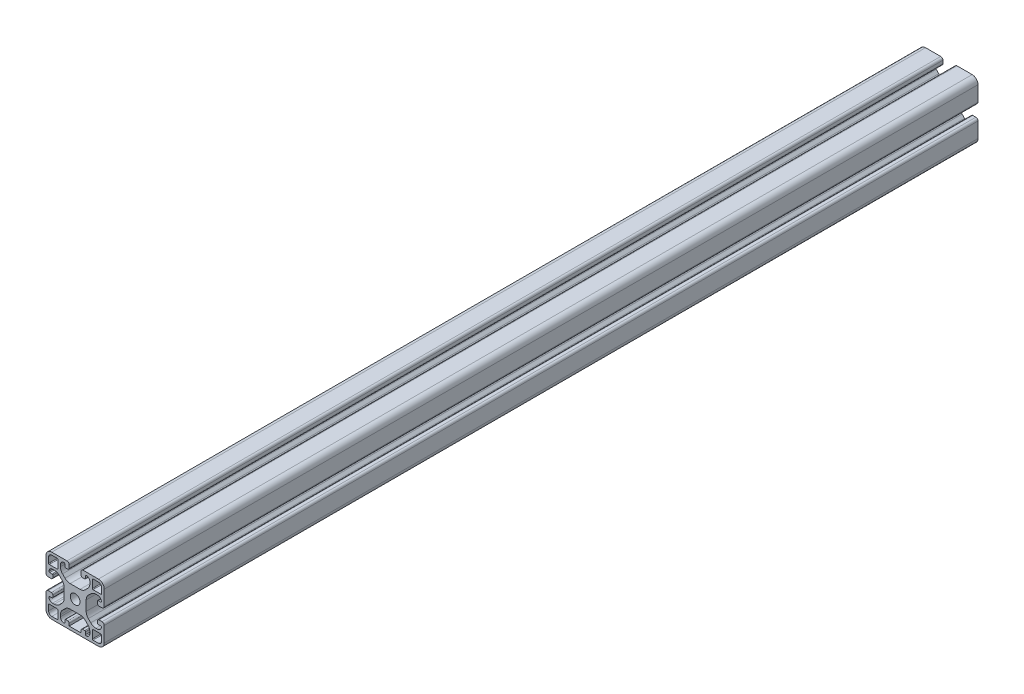
SolidWorks part; units mm, degrees
ref_plane "Ebene vorne" through (0, 0, 0) normal (0, 0, 1) x (1, 0, 0)
ref_plane "Ebene oben" through (0, 0, 0) normal (0, 1, 0) x (1, 0, 0)
ref_plane "Ebene rechts" through (0, 0, 0) normal (1, 0, 0) x (0, 0, -1)
ref_plane "Ebene1" through (0, 0, 1000) normal (0, 0, 1) x (1, 0, 0)
sketch "Skizze1" plane through (0, 0, 1000) normal (0, 0, 1) x (1, 0, 0)
  line L0 (27.8, 32.3) -> (27.8, 37.7)
  line L1 (28.3, 38.2) -> (32, 38.2)
  line L2 (34.2, 36) -> (34.2, 32.3)
  line L3 (33.7, 31.8) -> (28.3, 31.8)
  line L4 (28.3, 8.2) -> (33.7, 8.2)
  line L5 (34.2, 7.7) -> (34.2, 4)
  line L6 (32, 1.8) -> (28.3, 1.8)
  line L7 (27.8, 2.3) -> (27.8, 7.7)
  line L8 (3.7, 31.8) -> (-1.7, 31.8)
  line L9 (-2.2, 32.3) -> (-2.2, 36)
  line L10 (0, 38.2) -> (3.7, 38.2)
  line L11 (4.2, 37.7) -> (4.2, 32.3)
  line L12 (4.2, 7.7) -> (4.2, 2.3)
  line L13 (3.7, 1.8) -> (0, 1.8)
  line L14 (-2.2, 4) -> (-2.2, 7.7)
  line L15 (-1.7, 8.2) -> (3.7, 8.2)
  line L16 (20.1, 2) -> (11.9, 2)
  line L17 (11.9, 2) -> (11.9, 3.65)
  line L18 (10.9, 4.65) -> (9.4, 4.65)
  line L19 (8.9, 4.15) -> (8.9, 2.5)
  line L20 (5.9, 4.5) -> (5.9, 5.7076)
  line L21 (7.3645, 9.2431) -> (9.0569, 10.9355)
  line L22 (12.5924, 12.4) -> (19.4076, 12.4)
  line L23 (22.9431, 10.9355) -> (24.6355, 9.2431)
  line L24 (26.1, 5.7076) -> (26.1, 4.5)
  line L25 (23.1, 2.5) -> (23.1, 4.15)
  line L26 (22.6, 4.65) -> (21.1, 4.65)
  line L27 (20.1, 3.65) -> (20.1, 2)
  line L28 (5.9, 34.2924) -> (5.9, 35.5)
  line L29 (8.9, 37.5) -> (8.9, 35.85)
  line L30 (9.4, 35.35) -> (10.9, 35.35)
  line L31 (11.9, 36.35) -> (11.9, 38.5)
  line L32 (10.4, 40) -> (0, 40)
  line L33 (-4, 36) -> (-4, 25.6)
  line L34 (-2.5, 24.1) -> (-0.35, 24.1)
  line L35 (0.65, 25.1) -> (0.65, 26.6)
  line L36 (0.15, 27.1) -> (-1.5, 27.1)
  line L37 (0.5, 30.1) -> (1.7076, 30.1)
  line L38 (5.2431, 28.6355) -> (6.9355, 26.9431)
  line L39 (8.4, 23.4076) -> (8.4, 16.5924)
  line L40 (6.9355, 13.0569) -> (5.2431, 11.3645)
  line L41 (1.7076, 9.9) -> (0.5, 9.9)
  line L42 (-1.5, 12.9) -> (0.15, 12.9)
  line L43 (0.65, 13.4) -> (0.65, 14.9)
  line L44 (-0.35, 15.9) -> (-2.5, 15.9)
  line L45 (-4, 14.4) -> (-4, 4)
  line L46 (0, 0) -> (32, 0)
  line L47 (36, 4) -> (36, 14.4)
  line L48 (34.5, 15.9) -> (32.35, 15.9)
  line L49 (31.35, 14.9) -> (31.35, 13.4)
  line L50 (31.85, 12.9) -> (33.5, 12.9)
  line L51 (31.5, 9.9) -> (30.2924, 9.9)
  line L52 (26.7569, 11.3645) -> (25.0645, 13.0569)
  line L53 (23.6, 16.5924) -> (23.6, 23.4076)
  line L54 (25.0645, 26.9431) -> (26.7569, 28.6355)
  line L55 (30.2924, 30.1) -> (31.5, 30.1)
  line L56 (33.5, 27.1) -> (31.85, 27.1)
  line L57 (31.35, 26.6) -> (31.35, 25.1)
  line L58 (32.35, 24.1) -> (34.5, 24.1)
  line L59 (36, 25.6) -> (36, 36)
  line L60 (32, 40) -> (21.6, 40)
  line L61 (20.1, 38.5) -> (20.1, 36.35)
  line L62 (21.1, 35.35) -> (22.6, 35.35)
  line L63 (23.1, 35.85) -> (23.1, 37.5)
  line L64 (26.1, 35.5) -> (26.1, 34.2924)
  line L65 (24.6355, 30.7569) -> (22.9431, 29.0645)
  line L66 (19.4076, 27.6) -> (12.5924, 27.6)
  line L67 (9.0569, 29.0645) -> (7.3645, 30.7569)
  circle A0 centre (16, 20) radius 3.35
  arc A1 (28.3, 31.8) -> (27.8, 32.3) centre (28.3, 32.3) cw
  arc A2 (27.8, 37.7) -> (28.3, 38.2) centre (28.3, 37.7) cw
  arc A3 (32, 38.2) -> (34.2, 36) centre (32, 36) cw
  arc A4 (34.2, 32.3) -> (33.7, 31.8) centre (33.7, 32.3) cw
  arc A5 (27.8, 7.7) -> (28.3, 8.2) centre (28.3, 7.7) cw
  arc A6 (33.7, 8.2) -> (34.2, 7.7) centre (33.7, 7.7) cw
  arc A7 (34.2, 4) -> (32, 1.8) centre (32, 4) cw
  arc A8 (28.3, 1.8) -> (27.8, 2.3) centre (28.3, 2.3) cw
  arc A9 (4.2, 32.3) -> (3.7, 31.8) centre (3.7, 32.3) cw
  arc A10 (-1.7, 31.8) -> (-2.2, 32.3) centre (-1.7, 32.3) cw
  arc A11 (-2.2, 36) -> (0, 38.2) centre (0, 36) cw
  arc A12 (3.7, 38.2) -> (4.2, 37.7) centre (3.7, 37.7) cw
  arc A13 (3.7, 8.2) -> (4.2, 7.7) centre (3.7, 7.7) cw
  arc A14 (4.2, 2.3) -> (3.7, 1.8) centre (3.7, 2.3) cw
  arc A15 (0, 1.8) -> (-2.2, 4) centre (0, 4) cw
  arc A16 (-2.2, 7.7) -> (-1.7, 8.2) centre (-1.7, 7.7) cw
  arc A17 (11.9, 3.65) -> (10.9, 4.65) centre (10.9, 3.65) ccw
  arc A18 (9.4, 4.65) -> (8.9, 4.15) centre (9.4, 4.15) ccw
  arc A19 (8.9, 2.5) -> (8.4, 2) centre (8.4, 2.5) cw
  arc A20 (8.4, 2) -> (5.9, 4.5) centre (8.4, 4.5) cw
  arc A21 (5.9, 5.7076) -> (7.3645, 9.2431) centre (10.9, 5.7076) cw
  arc A22 (9.0569, 10.9355) -> (12.5924, 12.4) centre (12.5924, 7.4) cw
  arc A23 (19.4076, 12.4) -> (22.9431, 10.9355) centre (19.4076, 7.4) cw
  arc A24 (24.6355, 9.2431) -> (26.1, 5.7076) centre (21.1, 5.7076) cw
  arc A25 (26.1, 4.5) -> (23.6, 2) centre (23.6, 4.5) cw
  arc A26 (23.6, 2) -> (23.1, 2.5) centre (23.6, 2.5) cw
  arc A27 (23.1, 4.15) -> (22.6, 4.65) centre (22.6, 4.15) ccw
  arc A28 (21.1, 4.65) -> (20.1, 3.65) centre (21.1, 3.65) ccw
  arc A29 (7.3645, 30.7569) -> (5.9, 34.2924) centre (10.9, 34.2924) cw
  arc A30 (5.9, 35.5) -> (8.4, 38) centre (8.4, 35.5) cw
  arc A31 (8.4, 38) -> (8.9, 37.5) centre (8.4, 37.5) cw
  arc A32 (8.9, 35.85) -> (9.4, 35.35) centre (9.4, 35.85) ccw
  arc A33 (10.9, 35.35) -> (11.9, 36.35) centre (10.9, 36.35) ccw
  arc A34 (11.9, 38.5) -> (10.4, 40) centre (10.4, 38.5) ccw
  arc A35 (0, 40) -> (-4, 36) centre (0, 36) ccw
  arc A36 (-4, 25.6) -> (-2.5, 24.1) centre (-2.5, 25.6) ccw
  arc A37 (-0.35, 24.1) -> (0.65, 25.1) centre (-0.35, 25.1) ccw
  arc A38 (0.65, 26.6) -> (0.15, 27.1) centre (0.15, 26.6) ccw
  arc A39 (-1.5, 27.1) -> (-2, 27.6) centre (-1.5, 27.6) cw
  arc A40 (-2, 27.6) -> (0.5, 30.1) centre (0.5, 27.6) cw
  arc A41 (1.7076, 30.1) -> (5.2431, 28.6355) centre (1.7076, 25.1) cw
  arc A42 (6.9355, 26.9431) -> (8.4, 23.4076) centre (3.4, 23.4076) cw
  arc A43 (8.4, 16.5924) -> (6.9355, 13.0569) centre (3.4, 16.5924) cw
  arc A44 (5.2431, 11.3645) -> (1.7076, 9.9) centre (1.7076, 14.9) cw
  arc A45 (0.5, 9.9) -> (-2, 12.4) centre (0.5, 12.4) cw
  arc A46 (-2, 12.4) -> (-1.5, 12.9) centre (-1.5, 12.4) cw
  arc A47 (0.15, 12.9) -> (0.65, 13.4) centre (0.15, 13.4) ccw
  arc A48 (0.65, 14.9) -> (-0.35, 15.9) centre (-0.35, 14.9) ccw
  arc A49 (-2.5, 15.9) -> (-4, 14.4) centre (-2.5, 14.4) ccw
  arc A50 (-4, 4) -> (0, 0) centre (0, 4) ccw
  arc A51 (32, 0) -> (36, 4) centre (32, 4) ccw
  arc A52 (36, 14.4) -> (34.5, 15.9) centre (34.5, 14.4) ccw
  arc A53 (32.35, 15.9) -> (31.35, 14.9) centre (32.35, 14.9) ccw
  arc A54 (31.35, 13.4) -> (31.85, 12.9) centre (31.85, 13.4) ccw
  arc A55 (33.5, 12.9) -> (34, 12.4) centre (33.5, 12.4) cw
  arc A56 (34, 12.4) -> (31.5, 9.9) centre (31.5, 12.4) cw
  arc A57 (30.2924, 9.9) -> (26.7569, 11.3645) centre (30.2924, 14.9) cw
  arc A58 (25.0645, 13.0569) -> (23.6, 16.5924) centre (28.6, 16.5924) cw
  arc A59 (23.6, 23.4076) -> (25.0645, 26.9431) centre (28.6, 23.4076) cw
  arc A60 (26.7569, 28.6355) -> (30.2924, 30.1) centre (30.2924, 25.1) cw
  arc A61 (31.5, 30.1) -> (34, 27.6) centre (31.5, 27.6) cw
  arc A62 (34, 27.6) -> (33.5, 27.1) centre (33.5, 27.6) cw
  arc A63 (31.85, 27.1) -> (31.35, 26.6) centre (31.85, 26.6) ccw
  arc A64 (31.35, 25.1) -> (32.35, 24.1) centre (32.35, 25.1) ccw
  arc A65 (34.5, 24.1) -> (36, 25.6) centre (34.5, 25.6) ccw
  arc A66 (36, 36) -> (32, 40) centre (32, 36) ccw
  arc A67 (21.6, 40) -> (20.1, 38.5) centre (21.6, 38.5) ccw
  arc A68 (20.1, 36.35) -> (21.1, 35.35) centre (21.1, 36.35) ccw
  arc A69 (22.6, 35.35) -> (23.1, 35.85) centre (22.6, 35.85) ccw
  arc A70 (23.1, 37.5) -> (23.6, 38) centre (23.6, 37.5) cw
  arc A71 (23.6, 38) -> (26.1, 35.5) centre (23.6, 35.5) cw
  arc A72 (26.1, 34.2924) -> (24.6355, 30.7569) centre (21.1, 34.2924) cw
  arc A73 (22.9431, 29.0645) -> (19.4076, 27.6) centre (19.4076, 32.6) cw
  arc A74 (12.5924, 27.6) -> (9.0569, 29.0645) centre (12.5924, 32.6) cw
extrude "Aufsatz-Linear austragen1" add sketch "Skizze1" against normal blind 600
